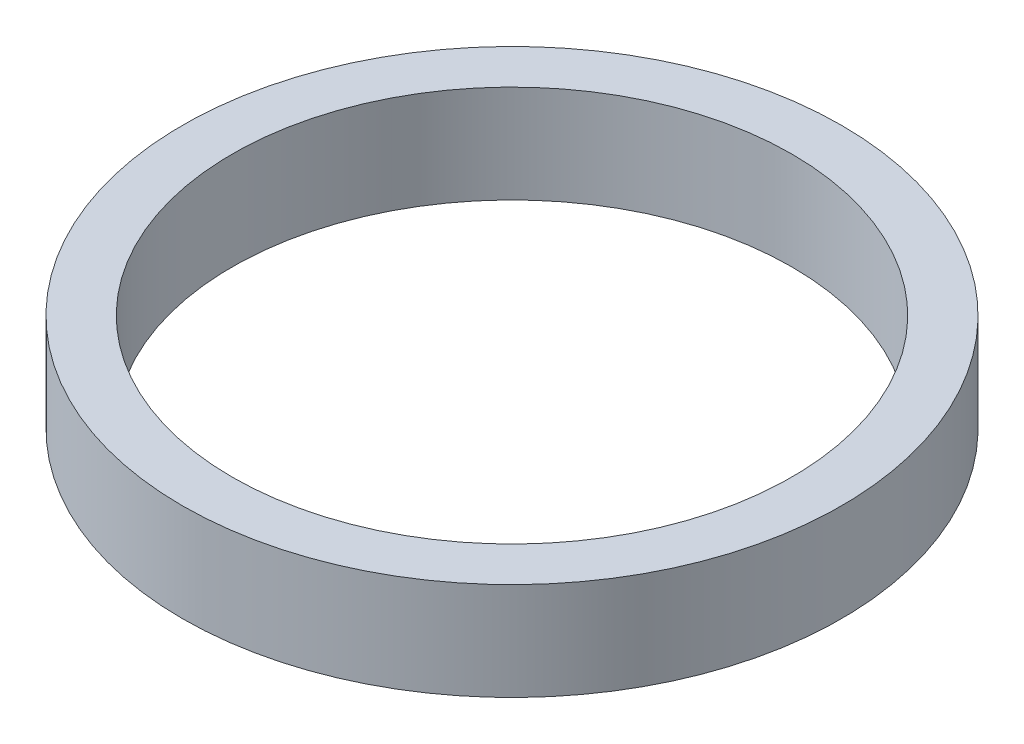
SolidWorks part; units mm, degrees
ref_plane "Front Plane" through (0, 0, 0) normal (0, 0, 1) x (1, 0, 0)
ref_plane "Top Plane" through (0, 0, 0) normal (0, 1, 0) x (1, 0, 0)
ref_plane "Right Plane" through (0, 0, 0) normal (1, 0, 0) x (0, 0, -1)
sketch "Sketch1" plane through (0, 0, 0) normal (0, 1, 0) x (1, 0, 0)
  circle A0 centre (0, 0) radius 19.55
  circle A1 centre (0, 0) radius 16.6
  dimension "D1" = 39.1
  dimension "D2" = 33.2
extrude "Boss-Extrude1" add sketch "Sketch1" along normal blind 5.8
